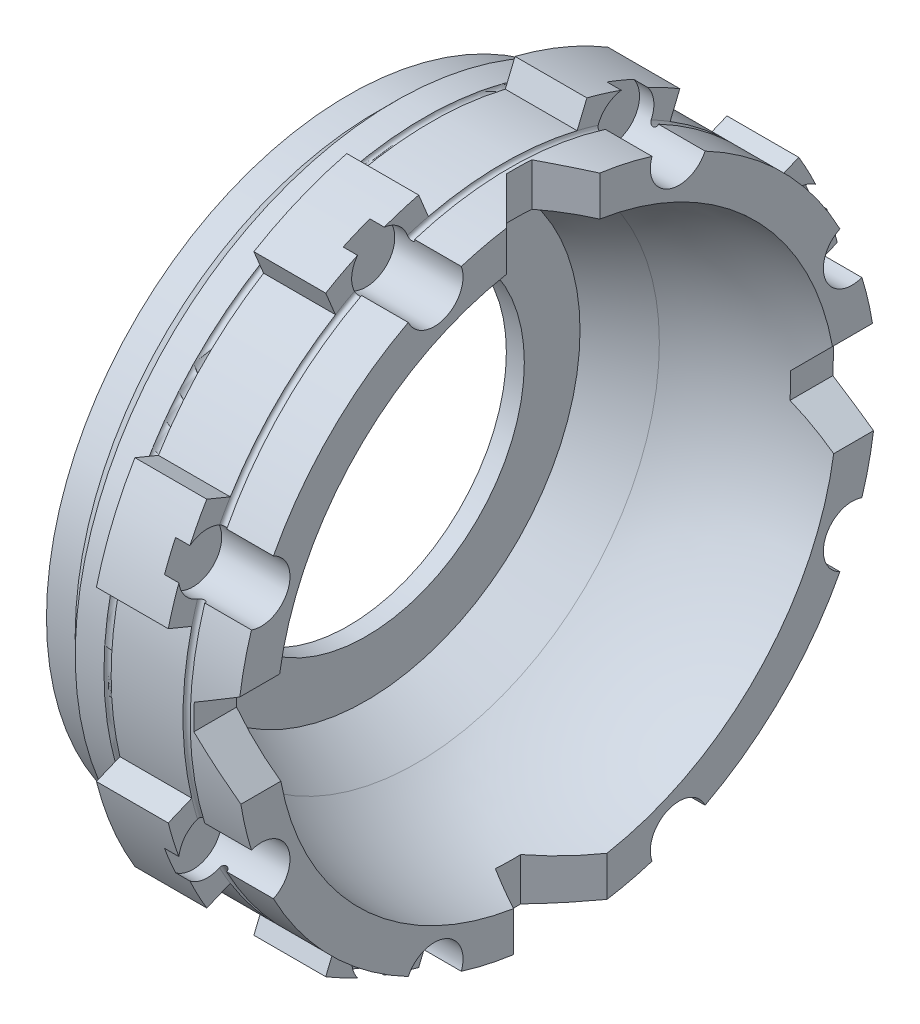
SolidWorks part; units mm, degrees
ref_plane "Přední rovina" through (0, 0, 0) normal (0, 0, 1) x (1, 0, 0)
ref_plane "Vrchní rovina" through (0, 0, 0) normal (0, 1, 0) x (1, 0, 0)
ref_plane "Pravá rovina" through (0, 0, 0) normal (1, 0, 0) x (0, 0, -1)
sketch "Skica1" plane through (0, 0, 0) normal (0, 0, 1) x (1, 0, 0)
  line L0 (0, 42) -> (4, 42)
  line L1 (4, 42) -> (6.5, 44.5)
  line L2 (6.5, 44.5) -> (29, 44.5)
  line L3 (29, 44.5) -> (29, 39.0165)
  line L4 (0, 22) -> (0, 42)
  line L5 (0, 22) -> (2.5, 22)
  line L6 (2.5, 22) -> (2.5, 29.75)
  line L7 (0, 0) -> (-52837.2145, 0) construction
  line L8 (0, 0) -> (0, 56.9694) construction
  line L9 (2.5, 29.75) -> (9.5, 33.7915)
  arc A1 (9.5, 33.7915) -> (29, 39.0165) centre (29, 0.0165) cw
  dimension "D9" = 39
  dimension "D1" = 84
  dimension "D2" = 89
  dimension "D3" = 2.5
  dimension "D4" = 4
  dimension "D5" = 29
  dimension "D6" = 44
  dimension "D7" = 59.5
  dimension "D8" = 30
  dimension "D10" = 7
  dimension "D11" = 26.5
revolve "Rotovat1" add sketch "Skica1" angle 360 about L7
sketch "Skica2" plane through (0, 0, 0) normal (0, 0, 1) x (1, 0, 0)
  line L0 (10.5, 44.5) -> (11.5, 44.5)
  line L1 (21.5, 44.5) -> (22.5, 44.5)
  line L2 (29, 44.5) -> (6.5, 44.5) construction
  line L3 (29, 44.5) -> (6.5, 44.5) construction
  line L4 (0, 42) -> (0, -42) construction
  line L5 (0, 0) -> (43.9834, 0) construction
  arc A0 (11.5, 44.5) -> (10.5, 44.5) centre (11, 44.5) cw
  arc A1 (22.5, 44.5) -> (21.5, 44.5) centre (22, 44.5) cw
  dimension "D1" = 0.5
  dimension "D2" = 0.5
  dimension "D3" = 11.5
  dimension "D4" = 10
revolve "Odebrat rotací1" cut sketch "Skica2" angle 360 about L5
ref_plane "Rovina1" through (21.5, 0, 0) normal (1, 0, 0) x (0, 0, -1)
ref_plane "Rovina2" through (11.5, 0, 0) normal (1, 0, 0) x (0, 0, -1)
sketch "Skica3" plane through (21.5, 0, 0) normal (1, 0, 0) x (0, 0, -1)
  line L0 (0, 0) -> (26.1983, 63.2483) construction
  line L3 (11.7053, 46.5509) -> (10.3502, 43.2796)
  line L5 (24.6396, 41.1933) -> (23.2846, 37.922)
  circle A0 centre (0, 0) radius 44.5 construction
  arc A1 (23.2846, 37.922) -> (10.3502, 43.2796) centre (0, 0) ccw
  arc A2 (24.6396, 41.1933) -> (11.7053, 46.5509) centre (0, 0) ccw
  point P4 (0, 44.5)
  dimension "D2" = 96
  dimension "D1" = 14
  dimension "D3" = 22.5
extrude "Přidat vysunutím1" add sketch "Skica3" against normal up to surface (10 mm away) up to plane "Rovina2"
sketch "Skica4" plane through (29, 0, 0) normal (1, 0, 0) x (0, 0, -1)
  line L0 (0, 58.5038) -> (0, 0) construction
  line L1 (0, 0) -> (17.0294, 41.1126) construction
  circle A0 centre (17.0294, 41.1126) radius 4
  circle A1 centre (0, 0) radius 44.5 construction
  circle A2 centre (0, 0) radius 44.5 construction
  dimension "D1" = 8
  dimension "D2" = 22.5
extrude "Odebrat vysunutím1" cut sketch "Skica4" against normal blind 9.5
pattern_circular "Kruhové pole1" count 8 over 360 about axis through (0, 0, 0) along (1, 0, 0) of "Přidat vysunutím1", "Odebrat vysunutím1"
ref_plane "Rovina3" through (0, 0, 44.5) normal (0, 0, 1) x (1, 0, 0)
sketch "Skica5" plane through (0, 0, 44.5) normal (0, 0, 1) x (1, 0, 0)
  line L0 (29, 6) -> (29, -7)
  line L1 (29, -7) -> (23, -1)
  line L2 (23, -1) -> (23, 2.5359)
  line L3 (23, 2.5359) -> (29, 6)
  line L4 (29, -39.4174) -> (29, -20.6524) construction
  line L5 (0, 0) -> (6.0562, 0) construction
  line L6 (0, 42) -> (0, -42) construction
  point P10 (23, -2.7733)
  point P11 (23, -0.7071)
  dimension "D1" = 1
  dimension "D2" = 60
  dimension "D3" = 45
  dimension "D4" = 6
  dimension "D5" = 6
extrude "Odebrat vysunutím2" cut sketch "Skica5" against normal blind 9.5
pattern_circular "Kruhové pole2" count 4 over 360 about axis through (0, 0, 0) along (1, 0, 0) of "Odebrat vysunutím2"
